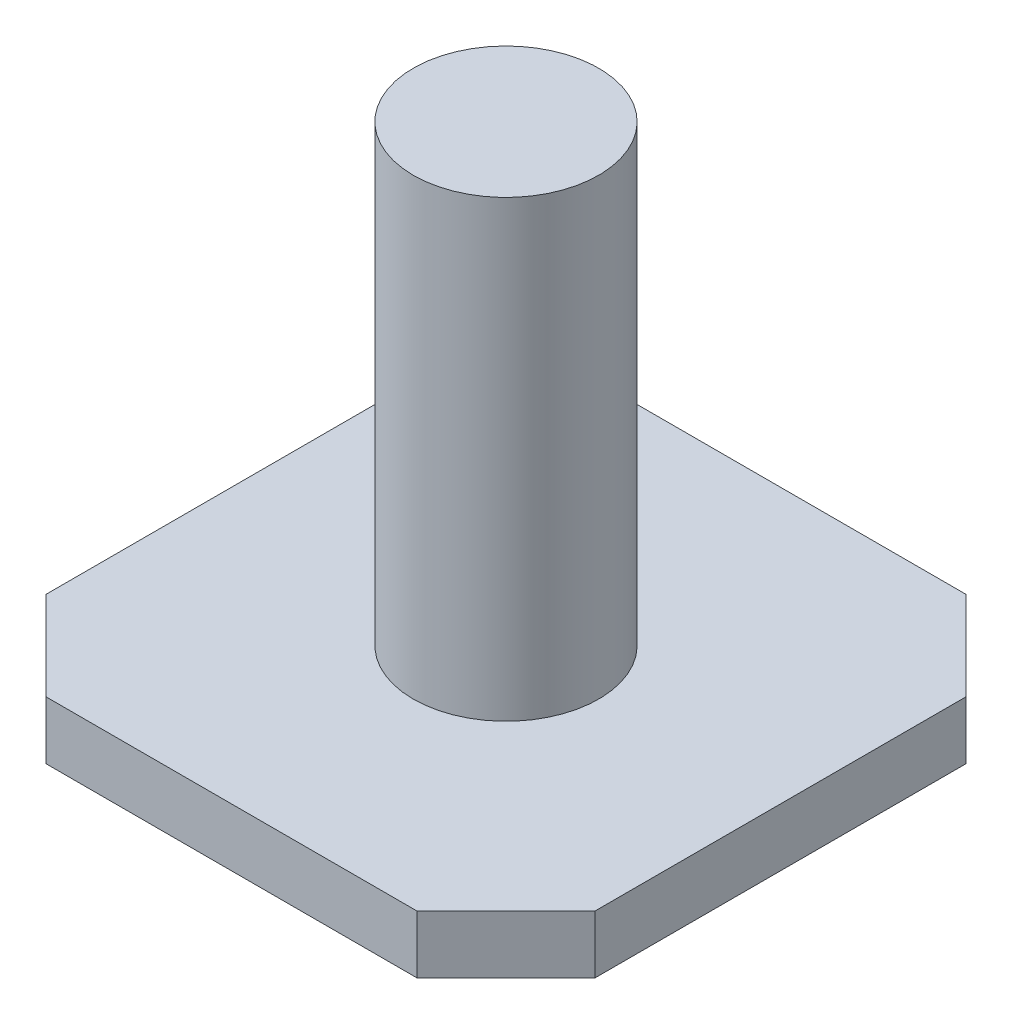
SolidWorks part; units mm, degrees
ref_plane "Front Plane" through (0, 0, 0) normal (0, 0, 1) x (1, 0, 0)
ref_plane "Top Plane" through (0, 0, 0) normal (0, 1, 0) x (1, 0, 0)
ref_plane "Right Plane" through (0, 0, 0) normal (1, 0, 0) x (0, 0, -1)
sketch "Sketch1" plane through (0, 0, 0) normal (0, 1, 0) x (1, 0, 0)
  line L5 (-9.017, 0) -> (9.017, 0) construction
  line L6 (0, 9.017) -> (0, -9.017) construction
  line L14 (-6.096, 9.017) -> (6.096, 9.017)
  line L15 (6.096, 9.017) -> (9.017, 6.096)
  line L16 (9.017, 6.096) -> (9.017, -6.096)
  line L17 (9.017, -6.096) -> (6.096, -9.017)
  line L18 (6.096, -9.017) -> (-6.096, -9.017)
  line L19 (-6.096, -9.017) -> (-9.017, -6.096)
  line L20 (-9.017, -6.096) -> (-9.017, 6.096)
  line L21 (-9.017, 6.096) -> (-6.096, 9.017)
  line L22 (6.096, 9.017) -> (6.096, -9.017) construction
  line L23 (9.017, 6.096) -> (-9.017, 6.096) construction
  point P0 (0, 0)
  point P8 (0, 9.1774)
  dimension "D1" = 12.192
  dimension "D2" = 45
  dimension "D3" = 18.034
extrude "Boss-Extrude1" add sketch "Sketch1" along normal blind 1.905
sketch "Sketch2" plane through (0, 1.905, 0) normal (0, 1, 0) x (1, 0, 0)
  circle A0 centre (0, 0) radius 3.048
  dimension "D1" = 6.096
extrude "Boss-Extrude2" add sketch "Sketch2" along normal blind 14.9098
